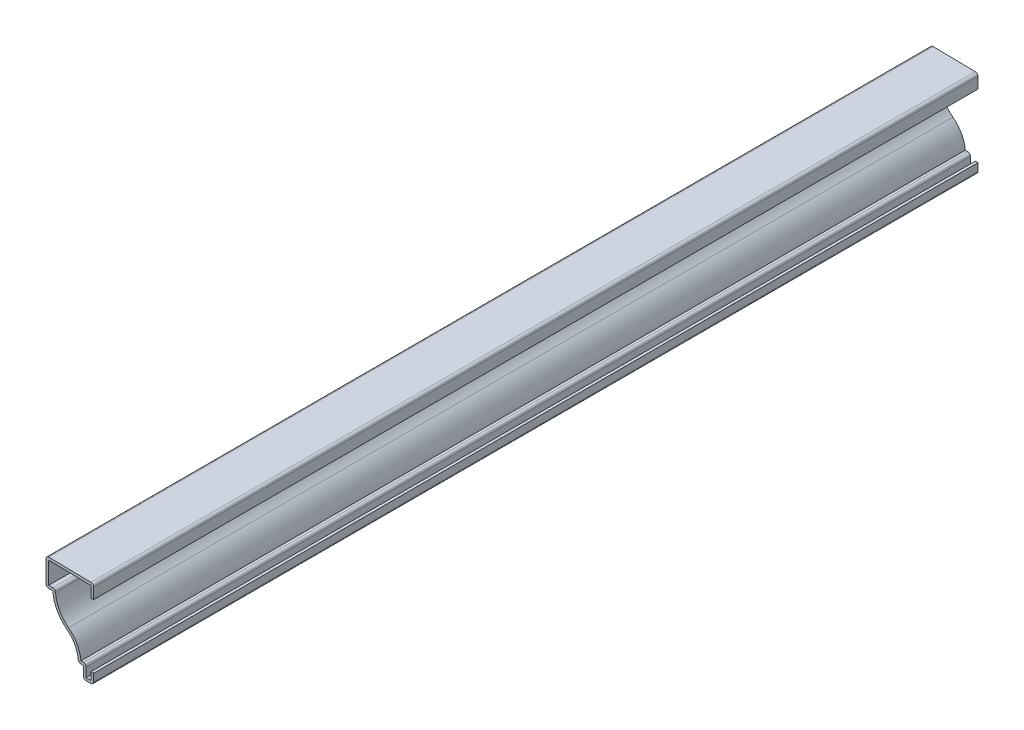
SolidWorks part; units mm, degrees
ref_plane "Front Plane" through (0, 0, 0) normal (0, 0, 1) x (1, 0, 0)
ref_plane "Top Plane" through (0, 0, 0) normal (0, 1, 0) x (1, 0, 0)
ref_plane "Right Plane" through (0, 0, 0) normal (1, 0, 0) x (0, 0, -1)
sketch "Sketch1" plane through (0, 0, 0) normal (0, 0, 1) x (1, 0, 0)
  line L0 (0, 4.7625) -> (0, 0)
  line L1 (0, 0) -> (-4.7625, 0)
  line L2 (-4.7625, 0) -> (-4.7625, 5.5562)
  line L3 (-4.7625, 5.5562) -> (-7.1438, 5.5562)
  line L4 (-19.05, 28.575) -> (-22.225, 28.575)
  line L5 (-22.225, 28.575) -> (-22.225, 41.275)
  line L6 (-22.225, 41.275) -> (0, 40.8781)
  line L7 (0, 40.8781) -> (0, 34.5281)
  line L8 (0, 34.5281) -> (0, 4.7625) construction
  arc A0 (-7.1438, 5.5562) -> (-12.4711, 16.2983) centre (-20.6375, 5.5562) ccw
  arc A1 (-12.4711, 16.2983) -> (-19.05, 28.575) centre (-2.3352, 29.6311) cw
  point P10 (0, 0)
  point P15 (0, 0)
  dimension "D11" = 13.4937
  dimension "D12" = 16.7481
  dimension "D1" = 41.275
  dimension "D2" = 22.225
  dimension "D3" = 12.7
  dimension "D4" = 6.35
  dimension "D5" = 29.7656
  dimension "D6" = 4.7625
  dimension "D7" = 3.175
  dimension "D8" = 4.7625
  dimension "D9" = 5.5562
  dimension "D10" = 2.3813
extrude "Extrude-Thin1" add sketch "Sketch1" against normal blind 412.75 thin
fillet "Fillet1" radius 1.27 8 edges at (0, 0, -206.375) (-4.7625, 0, -206.375) (-3.4925, 6.8262, -206.375) (-7.1438, 5.5562, -206.375) (-22.225, 28.575, -206.375) (-17.8119, 29.845, -206.375) (-22.225, 41.275, -206.375) (0, 40.8781, -206.375)
